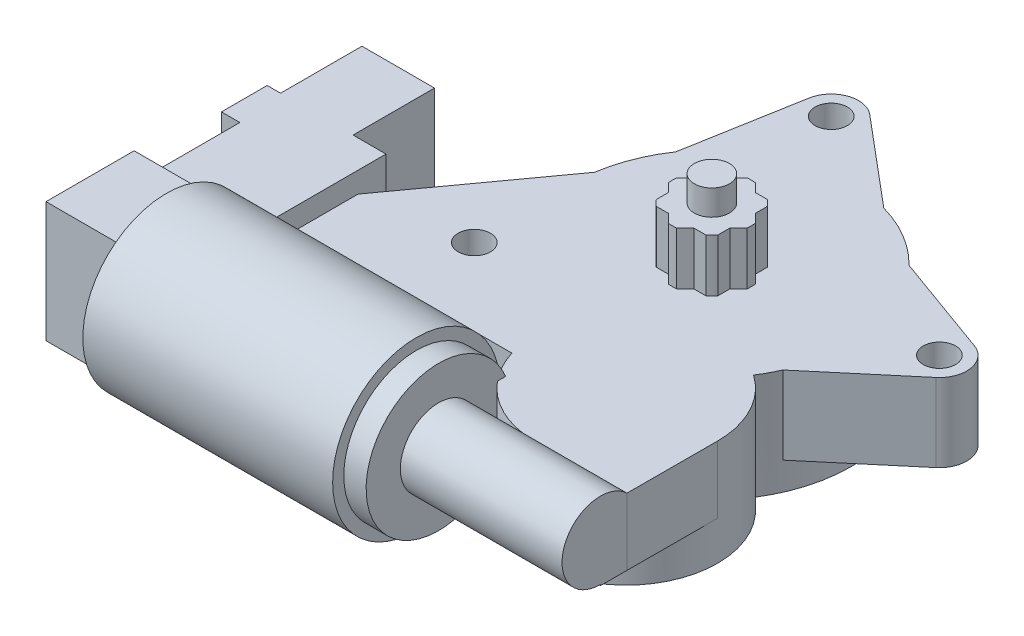
SolidWorks part; units mm, degrees
ref_plane "Front Plane" through (0, 0, 0) normal (0, 0, 1) x (1, 0, 0)
ref_plane "Top Plane" through (0, 0, 0) normal (0, 1, 0) x (1, 0, 0)
ref_plane "Right Plane" through (0, 0, 0) normal (1, 0, 0) x (0, 0, -1)
sketch "Sketch1" plane through (0, 0, 0) normal (0, 1, 0) x (1, 0, 0)
  circle A0 centre (0, 0) radius 31.75
  dimension "D1" = 63.5
extrude "Boss-Extrude1" add sketch "Sketch1" along normal blind 24.13 contours A0
sketch "Sketch2" plane through (0, 24.13, 0) normal (0, 1, 0) x (1, 0, 0)
  circle A0 centre (14.7757, -34.29) radius 20.828
  dimension "D1" = 41.656
  dimension "D2" = 37.338
  dimension "D3" = 34.29
extrude "Boss-Extrude2" add sketch "Sketch2" against normal blind 24.13
sketch "Sketch3" plane through (0, 0, 0) normal (1, 0, 0) x (0, 0, -1)
  line L0 (-17.2031, 24.13) -> (-55.118, 24.13) construction
  circle A0 centre (-60.96, 17.8435) radius 8.7249
  point P2 (-60.96, 26.5684)
  dimension "D1" = 2.4384
  dimension "D2" = 17.4498
  dimension "D3" = 60.96
extrude "Boss-Extrude3" add sketch "Sketch3" along normal blind 35.56 and the other way blind 1.27
sketch "Sketch4" plane through (-1.27, 0, 0) normal (-1, 0, 0) x (0, 0, 1)
  circle A0 centre (60.96, 17.8435) radius 16.51
  dimension "D1" = 33.02
extrude "Boss-Extrude4" add sketch "Sketch4" along normal blind 5.08
sketch "Sketch5" plane through (-6.35, 0, 0) normal (-1, 0, 0) x (0, 0, 1)
  circle A0 centre (60.96, 17.8435) radius 19.05
  dimension "D1" = 38.1
extrude "Boss-Extrude5" add sketch "Sketch5" along normal blind 56.896
sketch "Sketch6" plane through (-63.246, 0, 0) normal (-1, 0, 0) x (0, 0, 1)
  line L1 (50.927, 4.1275) -> (70.993, 4.1275)
  line L2 (50.927, 4.1275) -> (50.927, 31.5595)
  line L3 (50.927, 31.5595) -> (70.993, 31.5595)
  line L4 (70.993, 4.1275) -> (70.993, 31.5595)
  line L5 (50.927, 4.1275) -> (70.993, 31.5595) construction
  line L6 (50.927, 31.5595) -> (70.993, 4.1275) construction
  point P0 (60.96, 17.8435)
  dimension "D1" = 27.432
  dimension "D2" = 20.066
extrude "Boss-Extrude6" add sketch "Sketch6" along normal blind 17.399
sketch "Sketch7" plane through (0, 0, 50.927) normal (0, 0, -1) x (-1, 0, 0)
  line L1 (54.0258, 6.8326) -> (76.8858, 6.8326)
  line L2 (54.0258, 6.8326) -> (54.0258, 28.8544)
  line L3 (54.0258, 28.8544) -> (76.8858, 28.8544)
  line L4 (76.8858, 6.8326) -> (76.8858, 28.8544)
  line L5 (54.0258, 6.8326) -> (76.8858, 28.8544) construction
  line L6 (54.0258, 28.8544) -> (76.8858, 6.8326) construction
  line L7 (80.645, 31.5595) -> (80.645, 4.1275) construction
  point P0 (65.4558, 17.8435)
  point P8 (80.645, 17.8435)
  dimension "D1" = 3.7592
  dimension "D2" = 22.0218
  dimension "D3" = 22.86
extrude "Boss-Extrude7" add sketch "Sketch7" along normal blind 20.32 contours L4 L3 L2 L1
sketch "Sketch8" plane through (0, 0, 30.607) normal (0, 0, -1) x (-1, 0, 0)
  line L0 (54.0258, 6.8326) -> (54.0258, 28.8544)
  line L1 (54.0258, 6.8326) -> (81.0768, 6.8326)
  line L2 (54.0258, 28.8544) -> (81.0768, 28.8544)
  line L3 (81.0768, 6.8326) -> (81.0768, 28.8544)
  line L4 (76.8858, 6.8326) -> (76.8858, 28.8544) construction
  dimension "D1" = 4.191
extrude "Boss-Extrude8" add sketch "Sketch8" along normal blind 10.414
sketch "Sketch9" plane through (0, 0, 20.193) normal (0, 0, -1) x (-1, 0, 0)
  line L0 (81.0768, 28.8544) -> (54.0258, 28.8544) construction
  line L1 (78.0288, 28.8544) -> (61.5188, 28.8544)
  line L2 (78.0288, 28.8544) -> (78.0288, 8.5344)
  line L3 (78.0288, 8.5344) -> (61.5188, 8.5344)
  line L4 (61.5188, 28.8544) -> (61.5188, 8.5344)
  line L5 (81.0768, 6.8326) -> (81.0768, 28.8544) construction
  dimension "D1" = 20.32
  dimension "D2" = 3.048
  dimension "D3" = 16.51
extrude "Boss-Extrude9" add sketch "Sketch9" along normal blind 18.542
sketch "Sketch10" plane through (0, 0, 1.651) normal (0, 0, -1) x (-1, 0, 0)
  line L0 (78.0288, 8.5344) -> (78.0288, 28.8544) construction
  line L1 (76.581, 9.9822) -> (63.373, 9.9822)
  line L2 (76.581, 9.9822) -> (76.581, 23.6982)
  line L3 (76.581, 23.6982) -> (63.373, 23.6982)
  line L4 (63.373, 9.9822) -> (63.373, 23.6982)
  line L5 (61.5188, 8.5344) -> (78.0288, 8.5344) construction
  dimension "D1" = 13.208
  dimension "D2" = 13.716
  dimension "D3" = 1.4478
  dimension "D4" = 1.4478
extrude "Cut-Extrude1" cut sketch "Sketch10" against normal blind 18.542
sketch "Sketch11" plane through (0, 0, 0) normal (0, -1, 0) x (1, 0, 0)
  line L0 (-31.3989, -4.7085) -> (-54.0258, 26.543)
  line L1 (-54.0258, 20.193) -> (-54.0258, 45.4145) construction
  line L2 (-54.0258, 26.543) -> (-54.0258, 40.386)
  line L3 (-54.0258, 40.386) -> (-5.1402, 40.386)
  line L4 (-54.0258, 20.193) -> (-81.0768, 20.193) construction
  line L5 (-54.0258, 41.91) -> (-6.35, 41.91) construction
  line L6 (-25.717, -18.6198) -> (-36.9485, -3.1072) construction
  arc A0 (-5.8235, 31.2114) -> (26.6855, 17.2031) centre (0, 0) ccw construction
  arc A1 (26.6855, 17.2031) -> (-5.8235, 31.2114) centre (14.7757, 34.29) ccw construction
  arc A2 (-5.8235, 31.2114) -> (-31.3989, -4.7085) centre (0, 0) ccw
  arc A3 (-5.1402, 40.386) -> (-5.8235, 31.2114) centre (14.7757, 34.29) ccw
  dimension "D1" = 6.35
  dimension "D2" = 1.524
  dimension "D3" = 3.556
extrude "Boss-Extrude10" add sketch "Sketch11" against normal up to surface (17.78 mm away) from offset 6.35 contours L0 L2 L3 A3 A2 up to face at (4.721, 24.13, 35.4851) offset against normal yes
sketch "Sketch12" plane through (0, 24.13, 0) normal (0, 1, 0) x (1, 0, 0)
  line L0 (35.6037, -34.3342) -> (35.56, -54.9099)
  line L1 (35.56, -69.6849) -> (35.56, -52.2351) construction
  line L2 (35.56, -54.9099) -> (17.7127, -54.9099)
  arc A0 (17.7127, -54.9099) -> (26.6855, -17.2031) centre (14.7757, -34.29) ccw construction
  arc A1 (17.7127, -54.9099) -> (35.6037, -34.3342) centre (14.7757, -34.29) ccw
extrude "Boss-Extrude11" add sketch "Sketch12" against normal blind 15.24
sketch "Sketch13" plane through (0, 8.89, 0) normal (0, -1, 0) x (1, 0, 0)
  line L1 (35.56, 54.9099) -> (17.7127, 54.9099)
  line L2 (35.56, 54.9099) -> (35.56, 60.96)
  line L3 (35.56, 60.96) -> (17.7127, 60.96)
  line L4 (17.7127, 54.9099) -> (17.7127, 60.96)
  line L5 (-6.35, 41.91) -> (-6.35, 80.01) construction
  line L6 (-6.35, 41.91) -> (-6.35, 80.01)
  point P8 (-6.35, 60.96)
  line M7 (35.56, 54.9099) -> (17.7127, 54.9099)
extrude "Boss-Extrude12" add sketch "Sketch13" against normal blind 15.24 contours L4 L2 L3 M7
sketch "Sketch14" plane through (0, 24.13, 0) normal (0, 1, 0) x (1, 0, 0)
  line L0 (-26.194, 17.9425) -> (-21.6216, 43.7573)
  line L1 (46.0541, 13.7276) -> (22.7662, 22.1306)
  line L2 (-11.4902, 47.436) -> (8.5798, 30.5688)
  line L3 (29.0341, -12.8484) -> (47.9553, 3.118)
  arc A0 (26.6855, -17.2031) -> (-31.3989, 4.7085) centre (0, 0) ccw construction
  arc A1 (-21.6216, 43.7573) -> (-11.4902, 47.436) centre (-15.494, 42.672) cw
  circle A2 centre (-15.494, 42.672) radius 3.683
  circle A3 centre (43.942, 7.874) radius 3.683
  arc A4 (46.0541, 13.7276) -> (47.9553, 3.118) centre (43.942, 7.874) cw
  arc A5 (29.0341, -12.8484) -> (22.7662, 22.1306) centre (0, 0) ccw
  arc A6 (8.5798, 30.5688) -> (-26.194, 17.9425) centre (0, 0) ccw
  dimension "D2" = 7.366
  dimension "D3" = 2.54
  dimension "D8" = 2.54
  dimension "D1" = 60
  dimension "D4" = 42.672
  dimension "D5" = 15.494
  dimension "D6" = 43.942
  dimension "D7" = 7.874
  dimension "D9" = 60
extrude "Boss-Extrude13" add sketch "Sketch14" against normal blind 17.78
sketch "Sketch15" plane through (0, 24.13, 0) normal (0, 1, 0) x (1, 0, 0)
  circle A0 centre (-31.242, -22.86) radius 3.683
  circle A1 centre (-15.494, 42.672) radius 3.683 construction
  circle A2 centre (43.942, 7.874) radius 3.683 construction
  circle A3 centre (43.942, 7.874) radius 3.683
  circle A4 centre (-15.494, 42.672) radius 3.683
  point P9 (0, 0)
  dimension "D1" = 22.86
  dimension "D2" = 31.242
extrude "Cut-Extrude2" cut sketch "Sketch15" against normal through all
sketch "Sketch16" plane through (0, 24.13, 0) normal (0, 1, 0) x (1, 0, 0)
  circle A0 centre (0, 0) radius 4
  dimension "D1" = 8
extrude "Boss-Extrude14" add sketch "Sketch16" along normal blind 17.78
sketch "Sketch17" plane through (0, 24.13, 0) normal (0, 1, 0) x (1, 0, 0)
  line L0 (0, -9.8995) -> (-9.8995, 0)
  line L1 (-7, 7) -> (7, 7)
  line L2 (-7, 7) -> (-7, -7)
  line L3 (-7, -7) -> (7, -7)
  line L4 (7, 7) -> (7, -7)
  line L5 (-7, 7) -> (7, -7) construction
  line L6 (-7, -7) -> (7, 7) construction
  line L7 (0, -9.8995) -> (9.8995, 0)
  line L8 (-9.8995, 0) -> (0, 9.8995)
  line L9 (9.8995, 0) -> (0, 9.8995)
  line L10 (0, -9.8995) -> (0, 9.8995) construction
  line L11 (-9.8995, 0) -> (9.8995, 0) construction
  arc A0 (-5.6569, 7) -> (-7, 5.6569) centre (0, 0) ccw
  arc A1 (-8.9497, 0.9497) -> (-8.9497, -0.9497) centre (0, 0) ccw
  arc A2 (-7, -5.6569) -> (-5.6569, -7) centre (0, 0) ccw
  arc A3 (-0.9497, -8.9497) -> (0.9497, -8.9497) centre (0, 0) ccw
  arc A4 (5.6569, -7) -> (7, -5.6569) centre (0, 0) ccw
  arc A5 (8.9497, -0.9497) -> (8.9497, 0.9497) centre (0, 0) ccw
  arc A6 (7, 5.6569) -> (5.6569, 7) centre (0, 0) ccw
  arc A7 (0.9497, 8.9497) -> (-0.9497, 8.9497) centre (0, 0) ccw
  point P0 (0, 0)
  point P7 (0, 0)
  circle M11 centre (0, 0) radius 4
  dimension "D2" = 18
  dimension "D1" = 14
extrude "Boss-Extrude15" add sketch "Sketch17" along normal blind 12 contours L8 A1 L0 L2 | L4 L9 L1 L8 L2 L0 L3 L7 M11 | L1 A0 L2 L8 | L9 A7 L8 L1 | L4 A6 L1 L9 | L7 A5 L9 L4 | L3 A4 L4 L7 | L0 A3 L7 L3 | L2 A2 L3 L0
